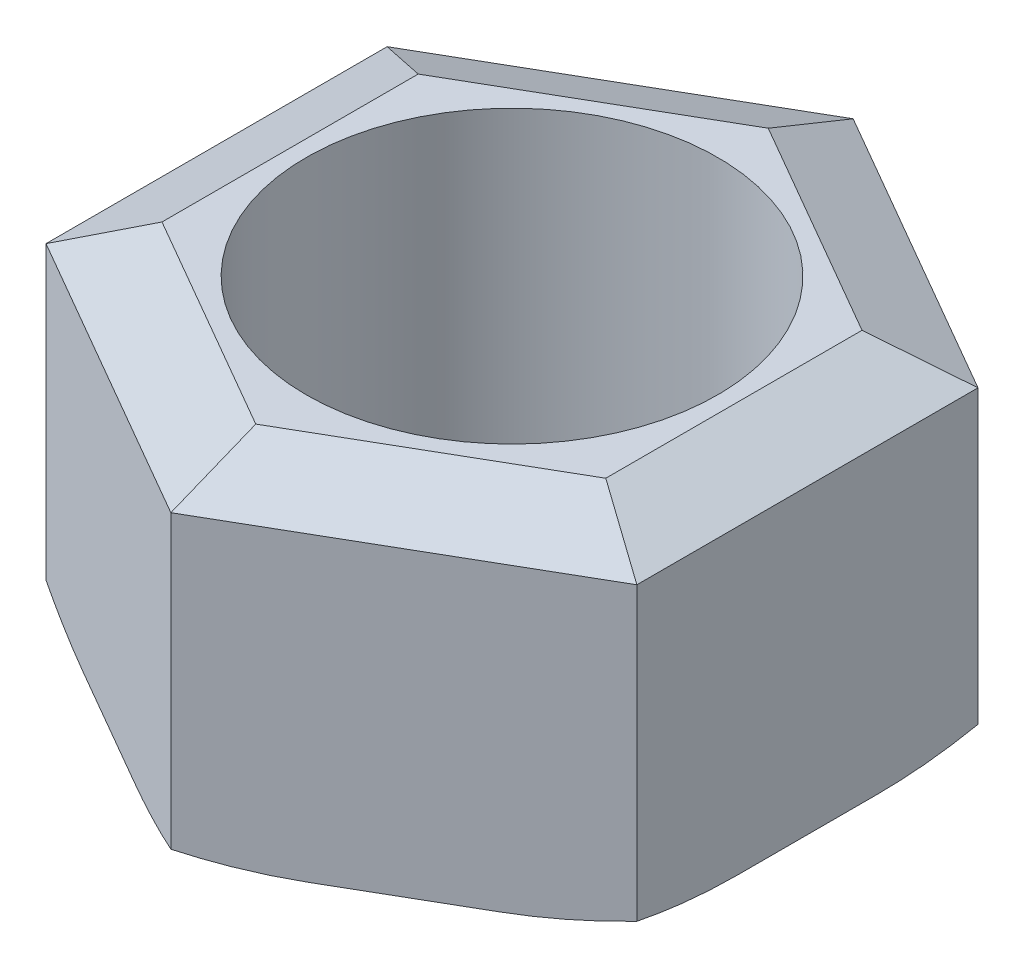
SolidWorks part; units mm, degrees
ref_plane "Спереди" through (0, 0, 0) normal (0, 0, 1) x (1, 0, 0)
ref_plane "Сверху" through (0, 0, 0) normal (0, 1, 0) x (1, 0, 0)
ref_plane "Справа" through (0, 0, 0) normal (1, 0, 0) x (0, 0, -1)
sketch "Эскиз1" plane through (0, 0, 0) normal (0, 1, 0) x (1, 0, 0)
  line L1 (0, 9.95) -> (-8.617, 4.975)
  line L2 (-8.617, 4.975) -> (-8.617, -4.975)
  line L3 (-8.617, -4.975) -> (0, -9.95)
  line L4 (0, -9.95) -> (8.617, -4.975)
  line L5 (8.617, -4.975) -> (8.617, 4.975)
  line L6 (8.617, 4.975) -> (0, 9.95)
  circle A0 centre (0, 0) radius 9.95 construction
  circle A1 centre (0, 0) radius 6
extrude "Бобышка-Вытянуть1" add sketch "Эскиз1" along normal blind 10.8
chamfer "Фаска1" distance 1 angle 65 6 edges at (8.617, 10.8, 0) (4.3085, 10.8, -7.4625) (-4.3085, 10.8, -7.4625) (-8.617, 10.8, 0) (-4.3085, 10.8, 7.4625) (4.3085, 10.8, 7.4625)
chamfer "Фаска2" distance 1 angle 65 6 edges at (-4.3085, 0, -7.4625) (4.3085, 0, -7.4625) (8.617, 0, 0) (4.3085, 0, 7.4625) (-4.3085, 0, 7.4625) (-8.617, 0, 0)
fillet "Скругление2" radius 12 6 edges at (0, 0.5, -8.7119) (-7.5447, 0.5, -4.3559) (-7.5447, 0.5, 4.3559) (0, 0.5, 8.7119) (7.5447, 0.5, 4.3559) (7.5447, 0.5, -4.3559)
